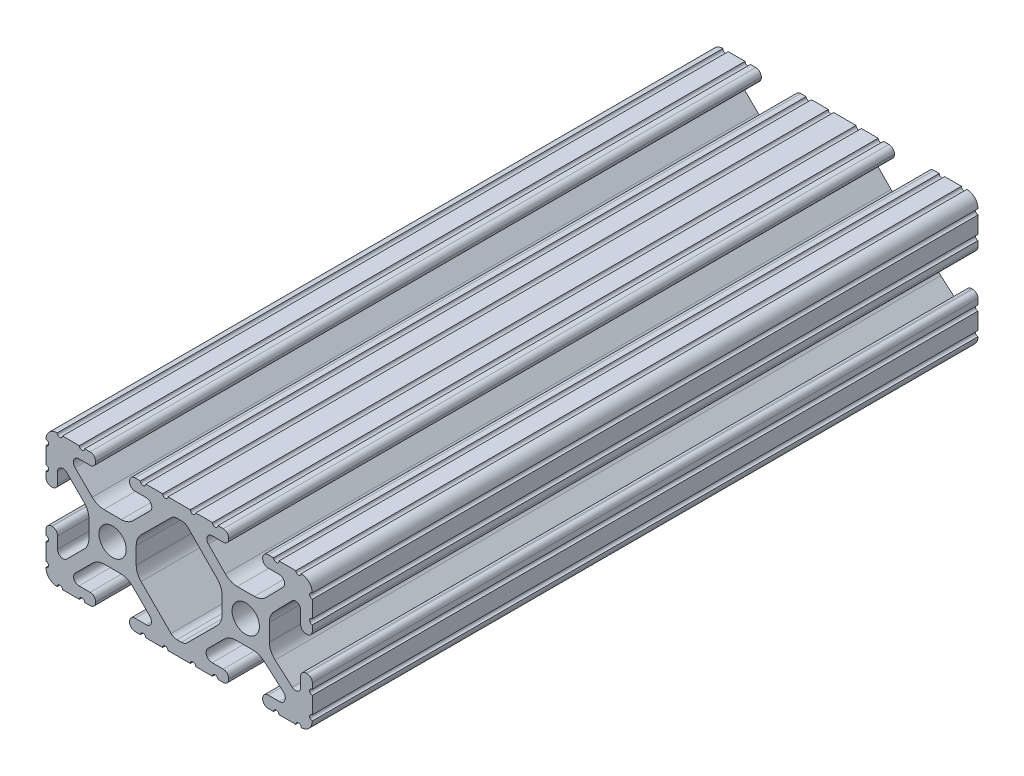
SolidWorks part; units mm, degrees
material "6061 Alloy"
ref_plane "Front Plane" through (0, 0, 0) normal (0, 0, 1) x (1, 0, 0)
ref_plane "Top Plane" through (0, 0, 0) normal (0, 1, 0) x (1, 0, 0)
ref_plane "Right Plane" through (0, 0, 0) normal (1, 0, 0) x (0, 0, -1)
sketch "Sketch1" plane through (0, 0, 0) normal (0, 0, 1) x (1, 0, 0)
  line L0 (-32.9707, 0) -> (32.2708, 0) construction
  line L1 (0, 12.7) -> (0, 0) construction
  line L2 (-12.7, 14.992) -> (-12.7, -12.6999) construction
  line L3 (12.7, 13.9801) -> (12.7, -13.3809) construction
  line L4 (-7.2595, -3.8694) -> (-1.5457, -9.5728)
  line L5 (1.5457, -9.5728) -> (7.2595, -3.8694)
  line L7 (-0.3952, 10.033) -> (0.5515, 10.033)
  line L9 (0.4332, -10.033) -> (-0.4332, -10.033)
  line L12 (8.1915, -1.6223) -> (8.1915, 1.6223)
  line L13 (7.2829, 3.8459) -> (1.6756, 9.5611)
  line L14 (-1.504, 9.5765) -> (-7.252, 3.8768)
  line L15 (-8.1915, 1.6223) -> (-8.1915, -1.6223)
  line L16 (22.2504, 12.7) -> (19.0331, 12.7)
  line L17 (18.0171, 12.7) -> (16.9875, 12.7)
  line L18 (15.9385, 11.651) -> (15.9385, 11.5392)
  line L19 (16.9875, 10.4902) -> (19.1164, 10.4902)
  line L20 (19.8441, 8.7652) -> (16.619, 5.4551)
  line L21 (14.3449, 4.4958) -> (11.0833, 4.4958)
  line L22 (8.817, 5.4472) -> (5.5642, 8.7627)
  line L23 (6.2894, 10.4902) -> (8.4125, 10.4902)
  line L24 (9.4615, 11.5392) -> (9.4615, 11.651)
  line L25 (8.4125, 12.7) -> (7.3829, 12.7)
  line L26 (6.3669, 12.7) -> (3.1496, 12.7)
  line L27 (2.1336, 12.7) -> (-2.1336, 12.7)
  line L28 (-3.1496, 12.7) -> (-6.3669, 12.7)
  line L29 (-7.3829, 12.7) -> (-8.4125, 12.7)
  line L30 (-9.4615, 11.651) -> (-9.4615, 11.5392)
  line L31 (-8.4125, 10.4902) -> (-6.2836, 10.4902)
  line L32 (-5.5326, 8.6661) -> (-8.81, 5.4163)
  line L33 (-11.0455, 4.4958) -> (-14.3545, 4.4958)
  line L34 (-16.59, 5.4163) -> (-19.8674, 8.6661)
  line L35 (-19.1164, 10.4902) -> (-16.9875, 10.4902)
  line L36 (-15.9385, 11.5392) -> (-15.9385, 11.651)
  line L37 (-16.9875, 12.7) -> (-18.0171, 12.7)
  line L38 (-19.0331, 12.7) -> (-22.2504, 12.7)
  line L39 (-25.4, 9.5504) -> (-25.4, 6.3331)
  line L40 (-25.4, 5.3171) -> (-25.4, 4.2375)
  line L41 (-24.401, 3.2385) -> (-24.2392, 3.2385)
  line L42 (-23.1902, 4.2875) -> (-23.1902, 6.3347)
  line L43 (-21.434, 7.0665) -> (-18.148, 3.8082)
  line L44 (-17.2085, 1.5536) -> (-17.2085, -1.6952)
  line L45 (-18.1405, -3.9423) -> (-21.4316, -7.2274)
  line L46 (-23.1902, -6.498) -> (-23.1902, -4.2875)
  line L47 (-24.2392, -3.2385) -> (-24.351, -3.2385)
  line L48 (-25.4, -4.2875) -> (-25.4, -5.3171)
  line L49 (-25.4, -6.3331) -> (-25.4, -9.5504)
  line L50 (-22.2504, -12.7) -> (-19.0331, -12.7)
  line L51 (-18.0171, -12.7) -> (-16.9875, -12.7)
  line L52 (-15.9384, -11.651) -> (-15.9384, -11.5392)
  line L53 (-16.9875, -10.4902) -> (-19.1164, -10.4902)
  line L54 (-19.8341, -8.7551) -> (-16.4966, -5.4237)
  line L55 (-14.2536, -4.4958) -> (-11.1464, -4.4958)
  line L56 (-8.9034, -5.4237) -> (-5.5659, -8.7551)
  line L57 (-6.2836, -10.4902) -> (-8.4125, -10.4902)
  line L58 (-9.4616, -11.5392) -> (-9.4616, -11.651)
  line L59 (-8.4125, -12.7) -> (-7.3829, -12.7)
  line L60 (-6.3669, -12.7) -> (-3.1496, -12.7)
  line L61 (-2.1336, -12.7) -> (2.1336, -12.7)
  line L62 (3.1496, -12.7) -> (6.3669, -12.7)
  line L63 (7.3829, -12.7) -> (8.4125, -12.7)
  line L64 (9.4616, -11.651) -> (9.4616, -11.5392)
  line L65 (8.4125, -10.4902) -> (6.2894, -10.4902)
  line L66 (5.4807, -8.5353) -> (8.5979, -5.4237)
  line L67 (10.8409, -4.4958) -> (14.1026, -4.4958)
  line L68 (16.1879, -5.2766) -> (19.8682, -8.4822)
  line L69 (19.1164, -10.4902) -> (16.9875, -10.4902)
  line L70 (15.9384, -11.5392) -> (15.9384, -11.651)
  line L71 (16.9875, -12.7) -> (18.0171, -12.7)
  line L72 (19.0331, -12.7) -> (22.2504, -12.7)
  line L73 (25.4, -9.5504) -> (25.4, -6.3331)
  line L74 (25.4, -5.3171) -> (25.4, -4.2375)
  line L75 (24.401, -3.2385) -> (24.1892, -3.2385)
  line L76 (23.1902, -4.2375) -> (23.1902, -6.1559)
  line L77 (21.584, -6.8869) -> (18.2982, -4.025)
  line L78 (17.2085, -1.6308) -> (17.2085, 1.6308)
  line L79 (18.1094, 3.8465) -> (21.5263, 7.3534)
  line L80 (23.1902, 6.6769) -> (23.1902, 4.2375)
  line L81 (24.1892, 3.2385) -> (24.401, 3.2385)
  line L82 (25.4, 4.2375) -> (25.4, 5.3171)
  line L83 (25.4, 6.3332) -> (25.4, 9.5504)
  circle A0 centre (-12.7, 0) radius 2.6035
  circle A1 centre (12.7, 0) radius 2.6035
  arc A2 (-0.3952, 10.033) -> (-1.504, 9.5765) centre (-0.3952, 8.4582) ccw
  arc A3 (0.5515, 10.033) -> (1.6756, 9.5611) centre (0.5515, 8.4582) cw
  arc A4 (-8.1915, -1.6223) -> (-7.2595, -3.8694) centre (-5.0165, -1.6223) ccw
  arc A5 (-0.4332, -10.033) -> (-1.5457, -9.5728) centre (-0.4332, -8.4582) cw
  arc A6 (7.2595, -3.8694) -> (8.1915, -1.6223) centre (5.0165, -1.6223) ccw
  arc A7 (8.1915, 1.6223) -> (7.2829, 3.8459) centre (5.0165, 1.6223) ccw
  arc A8 (0.4332, -10.033) -> (1.5457, -9.5728) centre (0.4332, -8.4582) ccw
  arc A9 (-7.252, 3.8768) -> (-8.1915, 1.6223) centre (-5.0165, 1.6223) ccw
  arc A16 (25.3998, 10.5664) -> (23.2664, 12.6998) centre (23.2918, 10.5918) ccw
  arc A17 (22.2504, 12.7) -> (23.2664, 12.6998) centre (22.7584, 12.7) ccw
  arc A18 (18.0171, 12.7) -> (19.0331, 12.7) centre (18.5251, 12.7) ccw
  arc A19 (16.9875, 12.7) -> (15.9385, 11.651) centre (16.9875, 11.651) ccw
  arc A20 (15.9385, 11.5392) -> (16.9875, 10.4902) centre (16.9875, 11.5392) ccw
  arc A21 (19.8441, 8.7652) -> (19.1164, 10.4902) centre (19.1164, 9.4742) ccw
  arc A22 (14.3449, 4.4958) -> (16.619, 5.4551) centre (14.3449, 7.6708) ccw
  arc A23 (8.817, 5.4472) -> (11.0833, 4.4958) centre (11.0833, 7.6708) ccw
  arc A24 (6.2894, 10.4902) -> (5.5642, 8.7627) centre (6.2894, 9.4742) ccw
  arc A25 (8.4125, 10.4902) -> (9.4615, 11.5392) centre (8.4125, 11.5392) ccw
  arc A26 (9.4615, 11.651) -> (8.4125, 12.7) centre (8.4125, 11.651) ccw
  arc A27 (6.3669, 12.7) -> (7.3829, 12.7) centre (6.8749, 12.7) ccw
  arc A28 (2.1336, 12.7) -> (3.1496, 12.7) centre (2.6416, 12.7) ccw
  arc A29 (-3.1496, 12.7) -> (-2.1336, 12.7) centre (-2.6416, 12.7) ccw
  arc A30 (-7.3829, 12.7) -> (-6.3669, 12.7) centre (-6.8749, 12.7) ccw
  arc A31 (-8.4125, 12.7) -> (-9.4615, 11.651) centre (-8.4125, 11.651) ccw
  arc A32 (-9.4615, 11.5392) -> (-8.4125, 10.4902) centre (-8.4125, 11.5392) ccw
  arc A33 (-5.5326, 8.6661) -> (-6.2836, 10.4902) centre (-6.2836, 9.4235) ccw
  arc A34 (-11.0455, 4.4958) -> (-8.81, 5.4163) centre (-11.0455, 7.6708) ccw
  arc A35 (-16.59, 5.4163) -> (-14.3545, 4.4958) centre (-14.3545, 7.6708) ccw
  arc A36 (-19.1164, 10.4902) -> (-19.8674, 8.6661) centre (-19.1164, 9.4235) ccw
  arc A37 (-16.9875, 10.4902) -> (-15.9385, 11.5392) centre (-16.9875, 11.5392) ccw
  arc A38 (-15.9385, 11.651) -> (-16.9875, 12.7) centre (-16.9875, 11.651) ccw
  arc A39 (-19.0331, 12.7) -> (-18.0171, 12.7) centre (-18.5251, 12.7) ccw
  arc A40 (-23.2664, 12.6998) -> (-22.2504, 12.7) centre (-22.7584, 12.7) ccw
  arc A41 (-23.2664, 12.6998) -> (-25.3998, 10.5664) centre (-23.2918, 10.5918) ccw
  arc A42 (-25.4, 9.5504) -> (-25.3998, 10.5664) centre (-25.4, 10.0584) ccw
  arc A43 (-25.4, 5.3171) -> (-25.4, 6.3331) centre (-25.4, 5.8251) ccw
  arc A44 (-25.4, 4.2375) -> (-24.401, 3.2385) centre (-24.401, 4.2375) ccw
  arc A45 (-24.2392, 3.2385) -> (-23.1902, 4.2875) centre (-24.2392, 4.2875) ccw
  arc A46 (-21.434, 7.0665) -> (-23.1902, 6.3347) centre (-22.1596, 6.3347) ccw
  arc A47 (-17.2085, 1.5536) -> (-18.148, 3.8082) centre (-20.3835, 1.5536) ccw
  arc A48 (-18.1405, -3.9423) -> (-17.2085, -1.6952) centre (-20.3835, -1.6952) ccw
  arc A49 (-23.1902, -6.498) -> (-21.4316, -7.2274) centre (-22.1596, -6.498) ccw
  arc A50 (-23.1902, -4.2875) -> (-24.2392, -3.2385) centre (-24.2392, -4.2875) ccw
  arc A51 (-24.351, -3.2385) -> (-25.4, -4.2875) centre (-24.351, -4.2875) ccw
  arc A52 (-25.4, -6.3331) -> (-25.4, -5.3171) centre (-25.4, -5.8251) ccw
  arc A53 (-25.3998, -10.5664) -> (-25.4, -9.5504) centre (-25.4, -10.0584) ccw
  arc A54 (-25.3998, -10.5664) -> (-23.2664, -12.6998) centre (-23.2918, -10.5918) ccw
  arc A55 (-22.2504, -12.7) -> (-23.2664, -12.6998) centre (-22.7584, -12.7) ccw
  arc A56 (-18.0171, -12.7) -> (-19.0331, -12.7) centre (-18.5251, -12.7) ccw
  arc A57 (-16.9875, -12.7) -> (-15.9384, -11.651) centre (-16.9875, -11.651) ccw
  arc A58 (-15.9384, -11.5392) -> (-16.9875, -10.4902) centre (-16.9875, -11.5392) ccw
  arc A59 (-19.8341, -8.7551) -> (-19.1164, -10.4902) centre (-19.1164, -9.4742) ccw
  arc A60 (-14.2536, -4.4958) -> (-16.4966, -5.4237) centre (-14.2536, -7.6708) ccw
  arc A61 (-8.9034, -5.4237) -> (-11.1464, -4.4958) centre (-11.1464, -7.6708) ccw
  arc A62 (-6.2836, -10.4902) -> (-5.5659, -8.7551) centre (-6.2836, -9.4742) ccw
  arc A63 (-8.4125, -10.4902) -> (-9.4616, -11.5392) centre (-8.4125, -11.5392) ccw
  arc A64 (-9.4616, -11.651) -> (-8.4125, -12.7) centre (-8.4125, -11.651) ccw
  arc A65 (-6.3669, -12.7) -> (-7.3829, -12.7) centre (-6.8749, -12.7) ccw
  arc A66 (-2.1336, -12.7) -> (-3.1496, -12.7) centre (-2.6416, -12.7) ccw
  arc A67 (3.1496, -12.7) -> (2.1336, -12.7) centre (2.6416, -12.7) ccw
  arc A68 (7.3829, -12.7) -> (6.3669, -12.7) centre (6.8749, -12.7) ccw
  arc A69 (8.4125, -12.7) -> (9.4616, -11.651) centre (8.4125, -11.651) ccw
  arc A70 (9.4616, -11.5392) -> (8.4125, -10.4902) centre (8.4125, -11.5392) ccw
  arc A71 (5.4807, -8.5353) -> (6.2894, -10.4902) centre (6.2894, -9.3455) ccw
  arc A72 (10.8409, -4.4958) -> (8.5979, -5.4237) centre (10.8409, -7.6708) ccw
  arc A73 (16.1879, -5.2766) -> (14.1026, -4.4958) centre (14.1026, -7.6708) ccw
  arc A74 (19.1164, -10.4902) -> (19.8682, -8.4822) centre (19.1164, -9.3455) ccw
  arc A75 (16.9875, -10.4902) -> (15.9384, -11.5392) centre (16.9875, -11.5392) ccw
  arc A76 (15.9384, -11.651) -> (16.9875, -12.7) centre (16.9875, -11.651) ccw
  arc A77 (19.0331, -12.7) -> (18.0171, -12.7) centre (18.5251, -12.7) ccw
  arc A78 (23.2664, -12.6998) -> (22.2504, -12.7) centre (22.7584, -12.7) ccw
  arc A79 (23.2664, -12.6998) -> (25.3998, -10.5664) centre (23.2918, -10.5918) ccw
  arc A80 (25.4, -9.5504) -> (25.3998, -10.5664) centre (25.4, -10.0584) ccw
  arc A81 (25.4, -5.3171) -> (25.4, -6.3331) centre (25.4, -5.8251) ccw
  arc A82 (25.4, -4.2375) -> (24.401, -3.2385) centre (24.401, -4.2375) ccw
  arc A83 (24.1892, -3.2385) -> (23.1902, -4.2375) centre (24.1892, -4.2375) ccw
  arc A84 (21.584, -6.8869) -> (23.1902, -6.1559) centre (22.2207, -6.1559) ccw
  arc A85 (17.2085, -1.6308) -> (18.2982, -4.025) centre (20.3835, -1.6308) ccw
  arc A86 (18.1094, 3.8465) -> (17.2085, 1.6308) centre (20.3835, 1.6308) ccw
  arc A87 (23.1902, 6.6769) -> (21.5263, 7.3534) centre (22.2207, 6.6769) ccw
  arc A88 (23.1902, 4.2375) -> (24.1892, 3.2385) centre (24.1892, 4.2375) ccw
  arc A89 (24.401, 3.2385) -> (25.4, 4.2375) centre (24.401, 4.2375) ccw
  arc A90 (25.4, 6.3332) -> (25.4, 5.3171) centre (25.4, 5.8251) ccw
  arc A91 (25.3998, 10.5664) -> (25.4, 9.5504) centre (25.4, 10.0584) ccw
  dimension "D1" = 5.207
  dimension "D6" = 6.477
  dimension "D7" = 14.859
  dimension "D14" = 1.5748
  dimension "D16" = 1.5748
  dimension "D15" = 3.175
  dimension "D2" = 25.4
  dimension "D3" = 50.8
  dimension "D4" = 25.4
  dimension "D5" = 8.2042
  dimension "D8" = 2.2098
  dimension "D9" = 2.2098
  dimension "D10" = 2.2098
  dimension "D11" = 2.2098
  dimension "D12" = 2.2098
  dimension "D13" = 6.477
extrude "Extrude1" add sketch "Sketch1" against normal blind 127
